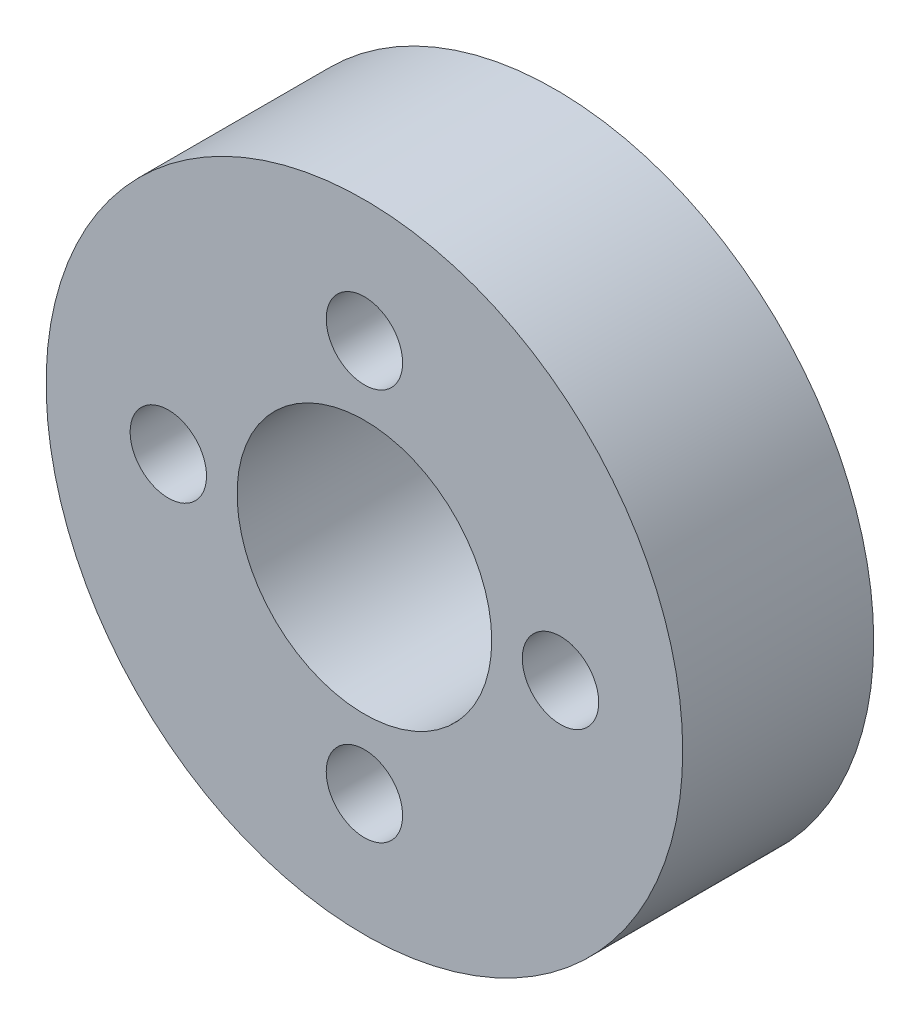
SolidWorks part; units mm, degrees
ref_plane "Front Plane" through (0, 0, 0) normal (0, 0, 1) x (1, 0, 0)
ref_plane "Top Plane" through (0, 0, 0) normal (0, 1, 0) x (1, 0, 0)
ref_plane "Right Plane" through (0, 0, 0) normal (1, 0, 0) x (0, 0, -1)
sketch "Sketch1" plane through (0, 0, 0) normal (0, 0, 1) x (1, 0, 0)
  circle A0 centre (0, 0) radius 15.875
  circle A1 centre (0, 0) radius 6.35
  dimension "D1" = 31.75
  dimension "D2" = 12.7
extrude "Boss-Extrude1" add sketch "Sketch1" along normal blind 9.525
sketch "Sketch2" plane through (0, 0, 9.525) normal (0, 0, 1) x (1, 0, 0)
  circle A0 centre (0, 9.779) radius 1.905
  dimension "D1" = 9.779
  dimension "D2" = 3.81
extrude "Cut-Extrude1" cut sketch "Sketch2" against normal up to vertex (9.525 mm away) up to point (0, 0, 0)
pattern_circular "CirPattern1" count 4 over 360 about axis through (0, 0, 0) along (0, 0, 1) of "Cut-Extrude1"
